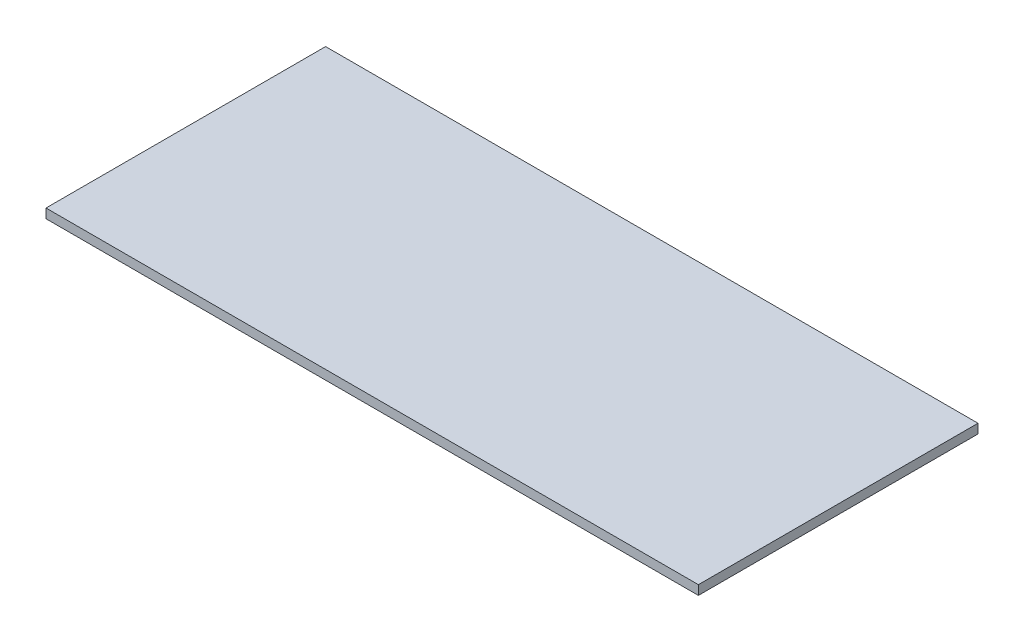
SolidWorks part; units mm, degrees
ref_plane "Front Plane" through (0, 0, 0) normal (0, 0, 1) x (1, 0, 0)
ref_plane "Top Plane" through (0, 0, 0) normal (0, 1, 0) x (1, 0, 0)
ref_plane "Right Plane" through (0, 0, 0) normal (1, 0, 0) x (0, 0, -1)
sketch "Sketch1" plane through (0, 0, 0) normal (0, 1, 0) x (1, 0, 0)
  line L1 (175, -75) -> (-175, -75)
  line L2 (175, -75) -> (175, 75)
  line L3 (175, 75) -> (-175, 75)
  line L4 (-175, -75) -> (-175, 75)
  line L5 (175, -75) -> (-175, 75) construction
  line L6 (175, 75) -> (-175, -75) construction
  point P0 (0, 0)
  dimension "D1" = 350
  dimension "D2" = 150
extrude "Boss-Extrude1" add sketch "Sketch1" along normal blind 5
